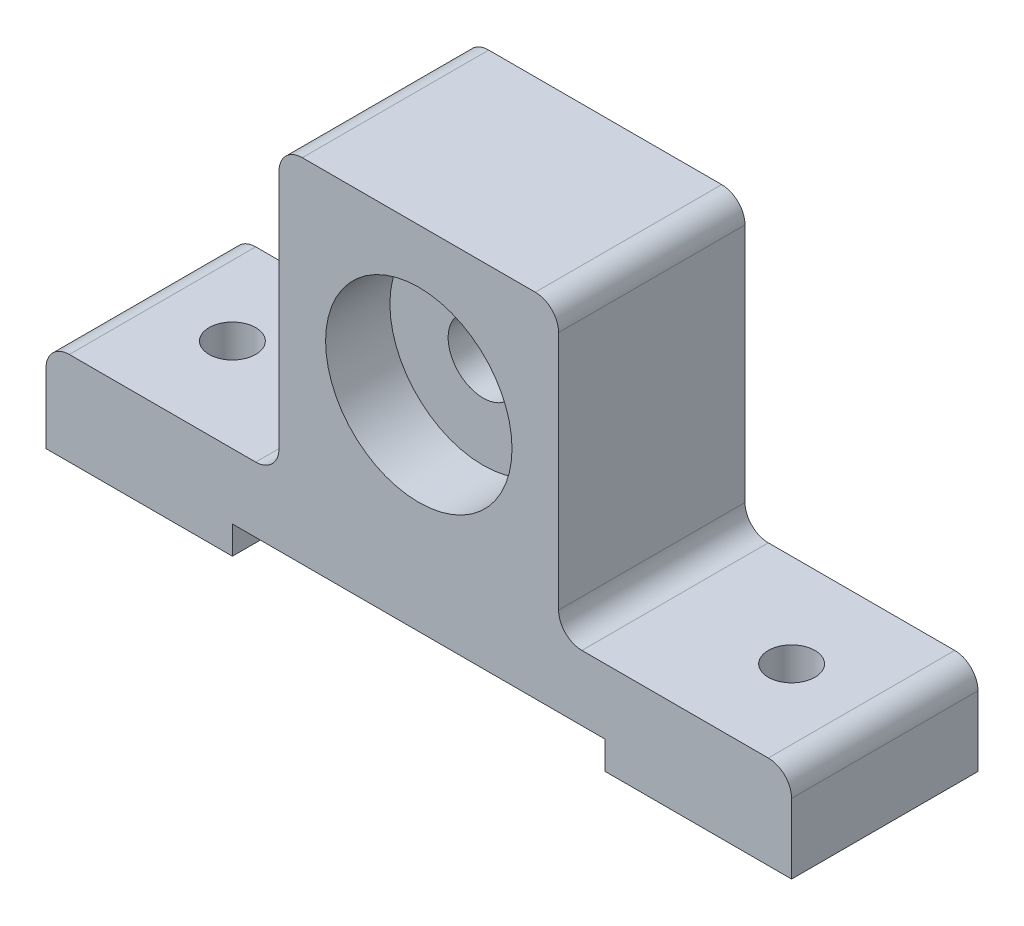
SolidWorks part; units mm, degrees
ref_plane "Front Plane" through (0, 0, 0) normal (0, 0, 1) x (1, 0, 0)
ref_plane "Top Plane" through (0, 0, 0) normal (0, 1, 0) x (1, 0, 0)
ref_plane "Right Plane" through (0, 0, 0) normal (1, 0, 0) x (0, 0, -1)
sketch "Sketch5" plane through (0, 0, 0) normal (0, 0, 1) x (1, 0, 0)
  line L0 (6.35, 25.4) -> (57.15, 25.4)
  line L1 (0, 0) -> (50.8, 0)
  line L2 (0, 0) -> (0, 19.05)
  line L3 (69.85, 103.5934) -> (133.35, 103.5934)
  line L4 (203.2, 0) -> (203.2, 19.05)
  line L5 (63.5, 31.75) -> (63.5, 97.2434)
  line L6 (139.7, 97.2434) -> (139.7, 31.75)
  line L7 (146.05, 25.4) -> (196.85, 25.4)
  line L8 (50.8, 0) -> (50.8, 7.62)
  line L9 (50.8, 7.62) -> (152.4, 7.62)
  line L10 (152.4, 7.62) -> (152.4, 0)
  line L11 (152.4, 0) -> (203.2, 0)
  arc A0 (139.7, 97.2434) -> (133.35, 103.5934) centre (133.35, 97.2434) ccw
  arc A1 (63.5, 97.2434) -> (69.85, 103.5934) centre (69.85, 97.2434) cw
  arc A2 (57.15, 25.4) -> (63.5, 31.75) centre (57.15, 31.75) ccw
  arc A3 (139.7, 31.75) -> (146.05, 25.4) centre (146.05, 31.75) ccw
  arc A4 (196.85, 25.4) -> (203.2, 19.05) centre (196.85, 19.05) cw
  arc A5 (6.35, 25.4) -> (0, 19.05) centre (6.35, 19.05) ccw
  point P16 (139.7, 103.5934)
  point P19 (63.5, 103.5934)
  point P22 (63.5, 25.4)
  point P27 (203.2, 25.4)
  point P30 (0, 25.4)
  dimension "D9" = 6.35
  dimension "D1" = 203.2
  dimension "D2" = 50.8
  dimension "D3" = 50.8
  dimension "D4" = 76.2
  dimension "D5" = 25.4
  dimension "D6" = 25.4
  dimension "D7" = 63.5
  dimension "D8" = 103.5934
  dimension "D10" = 7.62
extrude "Boss-Extrude1" add sketch "Sketch5" against normal blind 50.8
sketch "Sketch6" plane through (0, 0, 0) normal (0, 0, 1) x (1, 0, 0)
  circle A0 centre (101.6, 63.5) radius 9.525
  dimension "D1" = 19.05
  dimension "D2" = 38.1
  dimension "D3" = 63.5
extrude "Cut-Extrude1" cut sketch "Sketch6" against normal blind 50.8
sketch "Sketch7" plane through (0, 0, 0) normal (0, 0, 1) x (1, 0, 0)
  circle A0 centre (101.6, 63.5) radius 25.4
  dimension "D1" = 50.8
extrude "Cut-Extrude2" cut sketch "Sketch7" against normal blind 17.526
sketch "Sketch8" plane through (0, 25.4, 0) normal (0, 1, 0) x (1, 0, 0)
  circle A0 centre (25.4, 25.4) radius 6.35
  dimension "D3" = 12.7
  dimension "D1" = 25.4
  dimension "D2" = 25.4
extrude "Cut-Extrude3" cut sketch "Sketch8" against normal through all
sketch "Sketch9" plane through (0, 25.4, 0) normal (0, 1, 0) x (1, 0, 0)
  circle A0 centre (177.8, 25.4) radius 6.35
  dimension "D3" = 12.7
  dimension "D1" = 25.4
  dimension "D2" = 25.4
extrude "Cut-Extrude4" cut sketch "Sketch9" against normal through all
